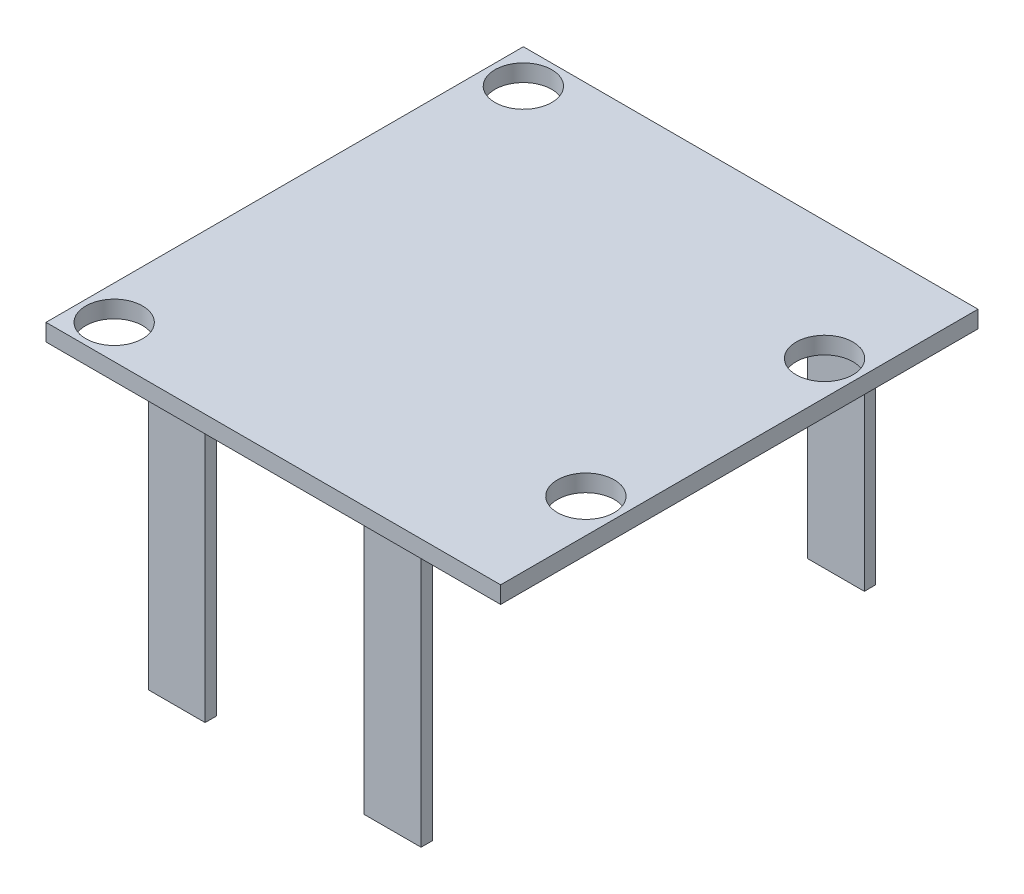
SolidWorks part; units mm, degrees
ref_plane "Front Plane" through (0, 0, 0) normal (0, 0, 1) x (1, 0, 0)
ref_plane "Top Plane" through (0, 0, 0) normal (0, 1, 0) x (1, 0, 0)
ref_plane "Right Plane" through (0, 0, 0) normal (1, 0, 0) x (0, 0, -1)
sketch "Sketch1" plane through (0, 0, 0) normal (0, 1, 0) x (1, 0, 0)
  line L1 (-200, 210) -> (200, 210)
  line L2 (-200, 210) -> (-200, -210)
  line L3 (-200, -210) -> (200, -210)
  line L4 (200, 210) -> (200, -210)
  line L5 (-200, 210) -> (200, -210) construction
  line L6 (-200, -210) -> (200, 210) construction
  point P0 (0, 0)
  dimension "D1" = 420
  dimension "D2" = 400
extrude "Boss-Extrude1" add sketch "Sketch1" along normal blind 15
sketch "Sketch2" plane through (0, 15, 0) normal (0, 1, 0) x (1, 0, 0)
  line L0 (-200, -210) -> (200, -210) construction
  line L2 (-200, 210) -> (-200, -210) construction
  line L3 (200, -210) -> (200, 210) construction
  circle A0 centre (-170, 180) radius 25
  circle A1 centre (-170, -180) radius 25
  circle A2 centre (170, -105) radius 25
  circle A3 centre (170, 105) radius 25
  dimension "D2" = 50
  dimension "D1" = 360
  dimension "D3" = 30
  dimension "D4" = 30
  dimension "D5" = 30
  dimension "D6" = 210
  dimension "D7" = 105
extrude "Cut-Extrude1" cut sketch "Sketch2" against normal up to surface (15 mm away) up to face at (0, 0, 0)
sketch "Sketch3" plane through (0, 0, 0) normal (0, -1, 0) x (1, 0, 0)
  line L1 (-120, 200) -> (-70, 200)
  line L2 (-120, 200) -> (-120, 190)
  line L3 (-120, 190) -> (-70, 190)
  line L4 (-70, 200) -> (-70, 190)
  line L6 (70, 200) -> (120, 200)
  line L7 (70, 200) -> (70, 190)
  line L8 (70, 190) -> (120, 190)
  line L9 (120, 200) -> (120, 190)
  line L10 (-120, -200) -> (-70, -200)
  line L11 (-120, -200) -> (-120, -190)
  line L12 (-120, -190) -> (-70, -190)
  line L13 (-70, -200) -> (-70, -190)
  line L14 (-200, -210) -> (-200, 210) construction
  line L15 (70, -200) -> (120, -200)
  line L16 (70, -200) -> (70, -190)
  line L17 (70, -190) -> (120, -190)
  line L18 (120, -200) -> (120, -190)
  line L19 (200, 210) -> (200, -210) construction
  line L21 (200, -210) -> (-200, -210) construction
  line L22 (-200, 210) -> (200, 210) construction
  dimension "D1" = 50
  dimension "D2" = 10
  dimension "D3" = 80
  dimension "D4" = 80
  dimension "D5" = 80
  dimension "D6" = 80
  dimension "D7" = 10
  dimension "D8" = 10
  dimension "D9" = 10
  dimension "D10" = 10
extrude "Boss-Extrude2" add sketch "Sketch3" along normal blind 230
